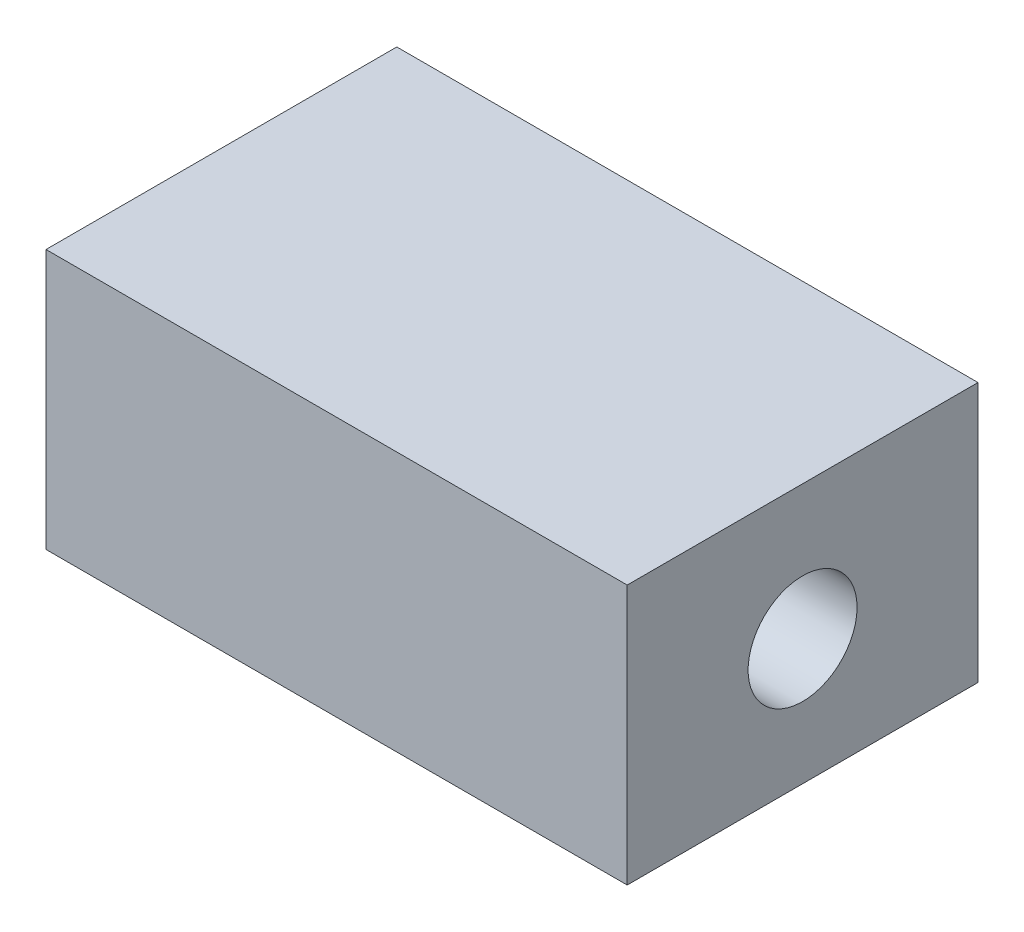
SolidWorks part; units mm, degrees
material "Copper"
ref_plane "Front Plane" through (0, 0, 0) normal (0, 0, 1) x (1, 0, 0)
ref_plane "Top Plane" through (0, 0, 0) normal (0, 1, 0) x (1, 0, 0)
ref_plane "Right Plane" through (0, 0, 0) normal (1, 0, 0) x (0, 0, -1)
sketch "Sketch1" plane through (0, 0, 0) normal (0, 1, 0) x (1, 0, 0)
  line L1 (-55.9257, 33.754) -> (55.9257, 33.754)
  line L2 (-55.9257, 33.754) -> (-55.9257, -33.754)
  line L3 (-55.9257, -33.754) -> (55.9257, -33.754)
  line L4 (55.9257, 33.754) -> (55.9257, -33.754)
  line L5 (-55.9257, 33.754) -> (55.9257, -33.754) construction
  line L6 (-55.9257, -33.754) -> (55.9257, 33.754) construction
  point P0 (0, 0)
extrude "Boss-Extrude1" add sketch "Sketch1" along normal blind 50
sketch "Sketch2" plane through (55.9257, 0, 0) normal (1, 0, 0) x (0, 0, -1)
  circle A0 centre (0, 24.1826) radius 10.4814
  point P2 (0, 24.1826)
extrude "Cut-Extrude1" cut sketch "Sketch2" against normal through all
ref_plane "Plane1" through (0, 0, 53.754) normal (0, 0, 1) x (1, 0, 0)
sketch "Sketch3" plane through (0, 0, 53.754) normal (0, 0, 1) x (1, 0, 0)
  line L0 (-31.754, 33.4276) -> (7.8256, 33.4276)
  line L1 (7.8256, 33.4276) -> (29.9481, 13.8635)
  line L2 (29.9481, 13.8635) -> (51.0172, 13.8635)
ref_plane "Plane2" through (0, -14.8716, 24.8561) normal (0, 0.5134, -0.8581) x (-1, 0, 0)
ref_plane "Plane3" through (7.8977, 21.7138, -2.997) normal (0.339, 0.932, -0.1286) x (0.9408, -0.3358, 0.0463)
